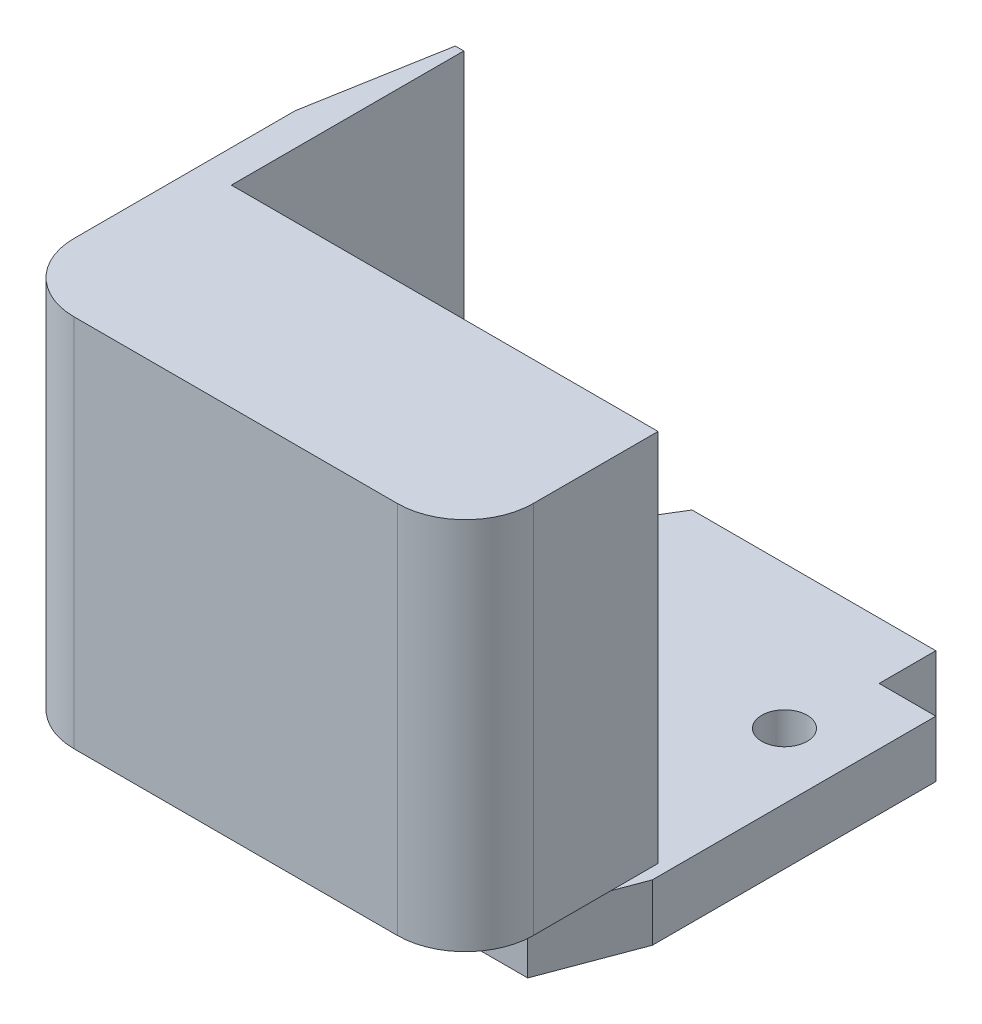
SolidWorks part; units mm, degrees
ref_plane "Front Plane" through (0, 0, 0) normal (0, 0, 1) x (1, 0, 0)
ref_plane "Top Plane" through (0, 0, 0) normal (0, 1, 0) x (1, 0, 0)
ref_plane "Right Plane" through (0, 0, 0) normal (1, 0, 0) x (0, 0, -1)
sketch "Sketch1" plane through (0, 0, 0) normal (0, 1, 0) x (1, 0, 0)
  line L0 (0, 0) -> (0, -45)
  line L1 (0, -45) -> (86, -45)
  line L2 (86, -45) -> (86, 31)
  line L3 (86, 31) -> (33, 31)
  line L4 (33, 31) -> (14, 0)
  line L5 (14, 0) -> (0, 0)
  dimension "D1" = 86
  dimension "D2" = 76
  dimension "D3" = 14
  dimension "D4" = 45
  dimension "D5" = 53
extrude "Boss-Extrude1" add sketch "Sketch1" along normal blind 10
chamfer "Chamfer1" distance 6 distance2 16 1 edges at (86, 5, 45)
chamfer "Chamfer2" distance 16 distance2 6 1 edges at (0, 5, 45)
sketch "Sketch2" plane through (0, 10, 0) normal (0, 1, 0) x (1, 0, 0)
  line L0 (86, 31) -> (33, 31) construction
  line L1 (76, 31) -> (86, 31)
  line L2 (76, 31) -> (76, 21)
  line L3 (76, 21) -> (86, 21)
  line L4 (86, 31) -> (86, 21)
  line L5 (86, -29) -> (86, 31) construction
  dimension "D1" = 10
  dimension "D2" = 10
extrude "Cut-Extrude1" cut sketch "Sketch2" against normal blind 10
sketch "Sketch3" plane through (0, 0, 0) normal (0, -1, 0) x (1, 0, 0)
  line L0 (44.7, 2.2979) -> (44.7, 11.7021)
  line L1 (43, 7) -> (43, 16.2907) construction
  line L2 (41.3, 2.2979) -> (41.3, 11.7021)
  arc A0 (41.3, 2.2979) -> (44.7, 2.2979) centre (43, 7) ccw
  arc A1 (44.7, 11.7021) -> (41.3, 11.7021) centre (43, 7) ccw
  dimension "D1" = 10
  dimension "D2" = 1.7
extrude "Boss-Extrude2" add sketch "Sketch3" along normal blind 7
sketch "Sketch4" plane through (0, -7, 0) normal (0, -1, 0) x (1, 0, 0)
  circle A0 centre (43, 7) radius 4.7
  circle A1 centre (43, 7) radius 5
  arc A2 (44.7, 11.7021) -> (41.3, 11.7021) centre (43, 7) ccw construction
  dimension "D1" = 9.4
extrude "Cut-Extrude2" cut sketch "Sketch4" against normal blind 3
sketch "Sketch5" plane through (0, 0, 0) normal (0, -1, 0) x (1, 0, 0)
  line L0 (86, 29) -> (86, -21) construction
  line L1 (6, 45) -> (80, 45) construction
  circle A0 centre (74.5, 35.5) radius 2.15
  circle A1 centre (11, 35.5) radius 2.15
  circle A2 centre (74.5, -5.8) radius 2.15
  dimension "D1" = 11.5
  dimension "D2" = 9.5
  dimension "D3" = 63.5
  dimension "D4" = 4.3
  dimension "D5" = 41.3
extrude "Cut-Extrude3" cut sketch "Sketch5" against normal through all
sketch "Sketch6" plane through (0, 10, 0) normal (0, 1, 0) x (1, 0, 0)
  circle A0 centre (74.5, 5.8) radius 4
  circle A1 centre (74.5, -35.5) radius 4
  circle A2 centre (11, -35.5) radius 4
  dimension "D1" = 8
extrude "Cut-Extrude4" cut sketch "Sketch6" against normal blind 6
sketch "Sketch7" plane through (0, 0, 0) normal (0, -1, 0) x (1, 0, 0)
  line L0 (43, 7) -> (63.6017, 7) construction
  line L1 (43, 7) -> (43, -6.2529) construction
  circle A0 centre (61.4, 7) radius 2.4
  circle A1 centre (24.6, 7) radius 2.4
  dimension "D1" = 18.4
  dimension "D2" = 4.8
extrude "Boss-Extrude3" add sketch "Sketch7" along normal blind 4.6
sketch "Sketch8" plane through (0, 0, -31) normal (0, 0, -1) x (-1, 0, 0)
  line L0 (-86, 0) -> (-86, 10) construction
  line L1 (-76, 0) -> (-33, 0) construction
  circle A0 centre (-43, 5) radius 1.65
  dimension "D2" = 5
  dimension "D3" = 3.3
  dimension "D1" = 43
extrude "Cut-Extrude5" cut sketch "Sketch8" against normal blind 10
sketch "Sketch10" plane through (0, 10, 0) normal (0, 1, 0) x (1, 0, 0)
  line L0 (0, 0) -> (0, -29) construction
  line L1 (15, -60) -> (72, -60)
  line L2 (3, -48) -> (3, -9)
  line L3 (8.7318, -26) -> (84, -26)
  line L4 (84, -48) -> (84, -26)
  line L5 (86, -29) -> (86, 21) construction
  line L6 (6, -45) -> (80, -45) construction
  line L10 (3, -9) -> (7.2318, 15)
  line L11 (7.2318, 15) -> (8.7318, 15)
  line L12 (8.7318, 15) -> (8.7318, -26)
  line L13 (14, 0) -> (0, 0) construction
  arc A0 (72, -60) -> (84, -48) centre (72, -48) ccw
  arc A1 (15, -60) -> (3, -48) centre (15, -48) cw
  dimension "D4" = 12
  dimension "D1" = 3
  dimension "D2" = 2
  dimension "D3" = 15
  dimension "D5" = 15
  dimension "D6" = 1.5
  dimension "D7" = 41
  dimension "D8" = 170
  dimension "D9" = 39
extrude "Boss-Extrude4" add sketch "Sketch10" along normal up to surface (66 mm away)
